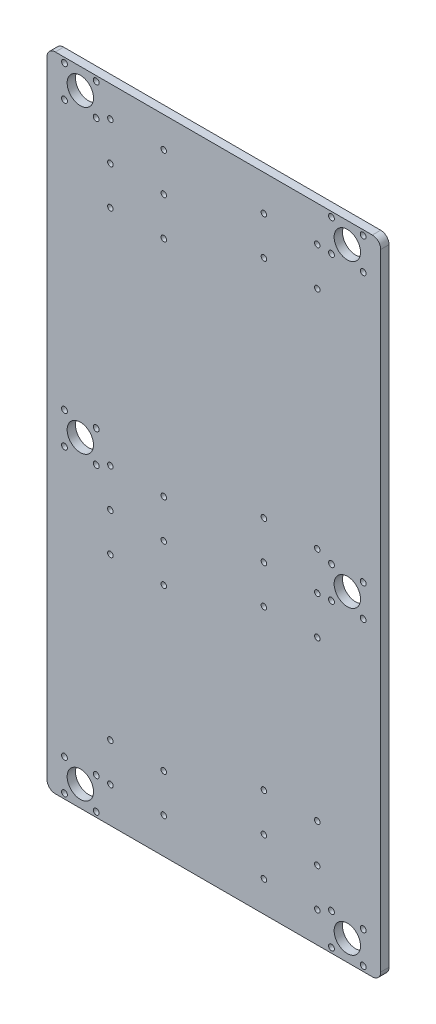
SolidWorks part; units mm, degrees
ref_plane "前视基准面" through (0, 0, 0) normal (0, 0, 1) x (1, 0, 0)
ref_plane "上视基准面" through (0, 0, 0) normal (0, 1, 0) x (1, 0, 0)
ref_plane "右视基准面" through (0, 0, 0) normal (1, 0, 0) x (0, 0, -1)
sketch "草图1" plane through (0, 0, 0) normal (0, 0, 1) x (1, 0, 0)
  line L0 (100, 180) -> (-100, 180) construction
  line L1 (100, -192.5) -> (-100, -192.5)
  line L2 (100, -192.5) -> (100, 192.5)
  line L3 (100, 192.5) -> (-100, 192.5)
  line L4 (-100, -192.5) -> (-100, 192.5)
  line L5 (0, 192.5) -> (0, -192.5) construction
  line L6 (100, 0) -> (-100, 0) construction
  line L7 (100, -180) -> (-100, -180) construction
  line L8 (-80, 180) -> (-80, -180) construction
  line L9 (80, 180) -> (80, -180) construction
  line L11 (-77.5, 172.5) -> (-82.5, 172.5) construction
  line L12 (-77.5, 172.5) -> (-77.5, 187.5) construction
  line L13 (-77.5, 187.5) -> (-82.5, 187.5) construction
  line L14 (-82.5, 172.5) -> (-82.5, 187.5) construction
  line L15 (-80, 187.5) -> (-80, 172.5) construction
  line L16 (-77.5, 180) -> (-82.5, 180) construction
  line L17 (-87.5, 182.5) -> (-72.5, 182.5) construction
  line L18 (-87.5, 182.5) -> (-87.5, 177.5) construction
  line L19 (-87.5, 177.5) -> (-72.5, 177.5) construction
  line L20 (-72.5, 182.5) -> (-72.5, 177.5) construction
  line L21 (-80, 177.5) -> (-80, 182.5) construction
  line L22 (-87.5, 180) -> (-72.5, 180) construction
  circle A0 centre (-80, 180) radius 7.9057
  circle A1 centre (-80, 0) radius 7.9057
  circle A2 centre (-80, -180) radius 7.9057
  circle A3 centre (80, -180) radius 7.9057
  circle A4 centre (80, 0) radius 7.9057
  circle A5 centre (80, 180) radius 7.9057
  circle A6 centre (-80, 180) radius 11 construction
  circle A23 centre (-30, 174.1657) radius 1.65
  circle A24 centre (-30, 151.1657) radius 1.65
  circle A25 centre (-30, 128.1657) radius 1.65
  circle A26 centre (-62, 128.1657) radius 1.65
  circle A27 centre (-62, 151.1657) radius 1.65
  circle A28 centre (-62, 174.1657) radius 1.65
  circle A29 centre (-30, -5.7024) radius 1.65
  circle A30 centre (-30, -28.7024) radius 1.65
  circle A31 centre (-30, -51.7024) radius 1.65
  circle A32 centre (-62, -51.7024) radius 1.65
  circle A33 centre (-62, -28.7024) radius 1.65
  circle A34 centre (-62, -5.7024) radius 1.65
  circle A35 centre (30, -128.1268) radius 1.65
  circle A36 centre (30, -151.1268) radius 1.65
  circle A37 centre (30, -174.1268) radius 1.65
  circle A38 centre (62, -174.1268) radius 1.65
  circle A39 centre (62, -151.1268) radius 1.65
  circle A58 centre (62, -128.1268) radius 1.65
  circle A59 centre (-30, -148.1204) radius 1.65
  circle A60 centre (-30, -171.1204) radius 1.65
  circle A61 centre (-62, -171.1204) radius 1.65
  circle A62 centre (-62, -148.1204) radius 1.65
  circle A63 centre (30, 13.15) radius 1.65
  circle A64 centre (30, -9.85) radius 1.65
  circle A65 centre (30, -32.85) radius 1.65
  circle A66 centre (62, -32.85) radius 1.65
  circle A67 centre (62, -9.85) radius 1.65
  circle A68 centre (62, 13.15) radius 1.65
  circle A69 centre (30, 171.1317) radius 1.65
  circle A70 centre (30, 148.1317) radius 1.65
  circle A71 centre (62, 148.1317) radius 1.65
  circle A72 centre (62, 171.1317) radius 1.65
  circle A73 centre (89.5, -170.5) radius 1.75 construction
  circle A74 centre (89.5, -189.5) radius 1.75 construction
  circle A75 centre (70.5, -189.5) radius 1.75 construction
  circle A76 centre (70.5, -170.5) radius 1.75 construction
  circle A77 centre (-70.5, -170.5) radius 1.75 construction
  circle A78 centre (-70.5, -189.5) radius 1.75 construction
  circle A79 centre (-89.5, -189.5) radius 1.75 construction
  circle A80 centre (-89.5, -170.5) radius 1.75 construction
  circle A81 centre (89.5, -9.5) radius 1.75 construction
  circle A82 centre (70.5, -9.5) radius 1.75 construction
  circle A83 centre (89.5, 9.5) radius 1.75 construction
  circle A84 centre (70.5, 9.5) radius 1.75 construction
  circle A85 centre (89.5, 170.5) radius 1.75 construction
  circle A86 centre (70.5, 170.5) radius 1.75 construction
  circle A87 centre (89.5, 189.5) radius 1.75 construction
  circle A88 centre (70.5, 189.5) radius 1.75 construction
  circle A89 centre (-70.5, 170.5) radius 1.75 construction
  circle A90 centre (-89.5, 170.5) radius 1.75 construction
  circle A91 centre (-70.5, 189.5) radius 1.75 construction
  circle A92 centre (-89.5, 189.5) radius 1.75 construction
  circle A93 centre (-89.5, -9.5) radius 1.75 construction
  circle A94 centre (-70.5, -9.5) radius 1.75 construction
  circle A95 centre (-70.5, 9.5) radius 1.75 construction
  circle A96 centre (-89.5, 9.5) radius 1.75 construction
  circle A97 centre (89.5, -170.5) radius 1.75
  circle A98 centre (89.5, -189.5) radius 1.75
  circle A99 centre (70.5, -189.5) radius 1.75
  circle A100 centre (70.5, -170.5) radius 1.75
  circle A101 centre (-70.5, -170.5) radius 1.75
  circle A102 centre (-70.5, -189.5) radius 1.75
  circle A103 centre (-89.5, -189.5) radius 1.75
  circle A104 centre (-89.5, -170.5) radius 1.75
  circle A105 centre (89.5, -9.5) radius 1.75
  circle A106 centre (70.5, -9.5) radius 1.75
  circle A107 centre (89.5, 9.5) radius 1.75
  circle A108 centre (70.5, 9.5) radius 1.75
  circle A109 centre (89.5, 170.5) radius 1.75
  circle A110 centre (70.5, 170.5) radius 1.75
  circle A111 centre (89.5, 189.5) radius 1.75
  circle A112 centre (70.5, 189.5) radius 1.75
  circle A113 centre (-70.5, 170.5) radius 1.75
  circle A114 centre (-89.5, 170.5) radius 1.75
  circle A115 centre (-70.5, 189.5) radius 1.75
  circle A116 centre (-89.5, 189.5) radius 1.75
  circle A117 centre (-89.5, -9.5) radius 1.75
  circle A118 centre (-70.5, -9.5) radius 1.75
  circle A119 centre (-70.5, 9.5) radius 1.75
  circle A120 centre (-89.5, 9.5) radius 1.75
  point P0 (0, 0)
  point P16 (0, 180)
  dimension "D9" = 3
  dimension "D10" = 22
  dimension "D1" = 200
  dimension "D2" = 385
  dimension "D3" = 180
  dimension "D4" = 80
  dimension "D5" = 5
  dimension "D6" = 15
  dimension "D7" = 5
  dimension "D8" = 15
extrude "凸台-拉伸1" add sketch "草图1" along normal blind 5
fillet "圆角1" radius 5 4 edges at (100, 192.5, 2.5) (100, -192.5, 2.5) (-100, -192.5, 2.5) (-100, 192.5, 2.5)
ref_plane "基准面1" through (0, 0, 0) normal (-1, 0, 0) x (0, 0, 1)
